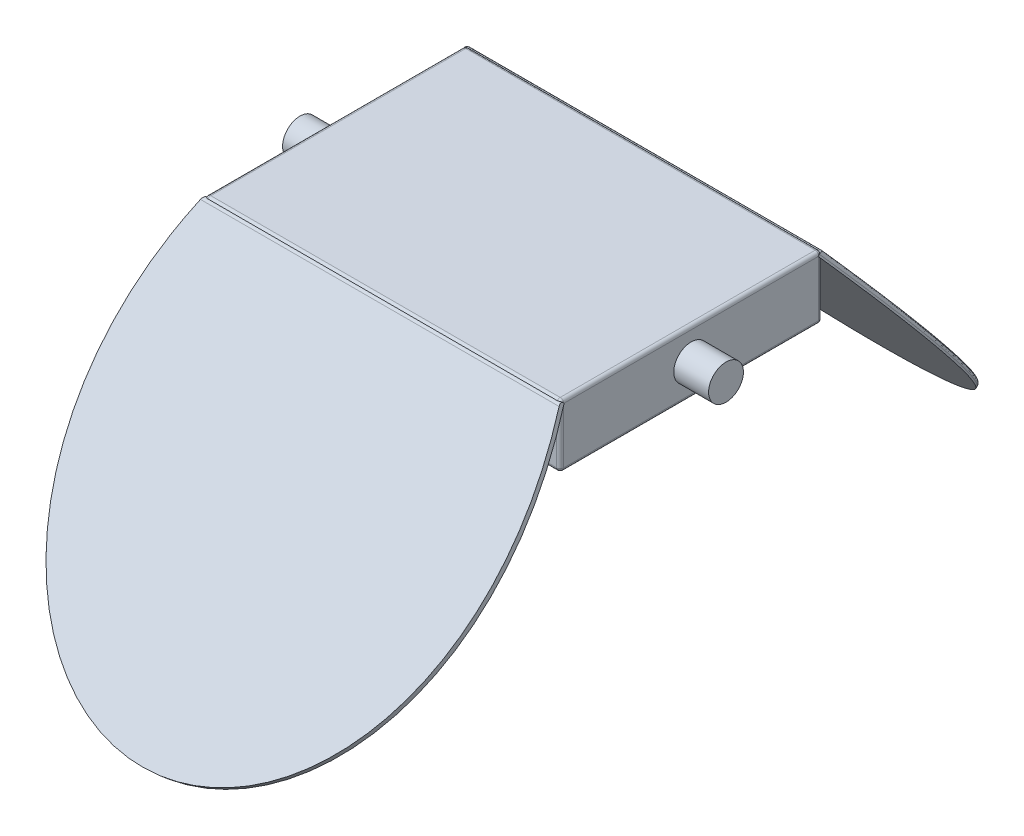
SolidWorks part; units mm, degrees
ref_plane "Front Plane" through (0, 0, 0) normal (0, 0, 1) x (1, 0, 0)
ref_plane "Top Plane" through (0, 0, 0) normal (0, 1, 0) x (1, 0, 0)
ref_plane "Right Plane" through (0, 0, 0) normal (1, 0, 0) x (0, 0, -1)
sketch "Sketch14" plane through (0, 0, 0) normal (0, 1, 0) x (1, 0, 0)
  line L1 (-129.921, -95.504) -> (129.921, -95.504)
  line L2 (-129.921, -95.504) -> (-129.921, 95.504)
  line L3 (-129.921, 95.504) -> (129.921, 95.504)
  line L4 (129.921, -95.504) -> (129.921, 95.504)
  line L5 (-129.921, -95.504) -> (129.921, 95.504) construction
  line L6 (-129.921, 95.504) -> (129.921, -95.504) construction
  point P0 (0, 0)
  dimension "D1" = 191.008
  dimension "D2" = 259.842
extrude "Boss-Extrude1" add sketch "Sketch14" along normal blind 45.72
ref_plane "Plane1" through (0, 65.9169, 78.5568) normal (0, 0.6428, 0.766) x (1, 0, 0)
sketch "Sketch15" plane through (0, 65.9169, 78.5568) normal (0, 0.6428, 0.766) x (1, 0, 0)
  line L1 (-129.921, -26.3652) -> (129.921, -26.3652)
  spline S0 degree 2 poles (129.921, -26.3652) (130.1193, -26.959) (133.7839, -37.9305) (136.4484, -48.414) (139.1256, -58.9474) (140.9759, -69.5188) (142.8478, -80.2142) (143.86, -90.8733) (144.8921, -101.742) (145.0222, -112.4895) (145.1556, -123.5085) (144.3397, -134.3066) (143.5138, -145.2361) (141.723, -155.8378) (139.899, -166.6356) (137.0925, -176.9833) (135.6607, -182.2625) (133.9783, -187.403) (132.2656, -192.6362) (130.2982, -197.7097) (128.3121, -202.8317) (126.0726, -207.7745) (123.8166, -212.754) (121.3108, -217.5351) (118.7774, -222.3688) (115.9974, -226.9827) (113.1758, -231.6657) (110.1105, -236.1049) (106.9856, -240.6304) (103.6196, -244.8844) (100.1934, -249.2145) (96.5317, -253.2451) (92.8443, -257.3039) (88.9341, -261.0412) (84.981, -264.8194) (80.818, -268.2516) (76.5881, -271.7389) (72.1617, -274.852) (67.6438, -278.0296) (62.9439, -280.8011) (58.2169, -283.5885) (53.3307, -285.9502) (48.429, -288.3194) (43.3933, -290.2474) (38.3138, -292.1921) (33.1257, -293.6768) (27.8617, -295.1833) (22.516, -296.2075) (17.109, -297.2434) (11.65, -297.7795) (6.2272, -298.3121) (0.785, -298.348) (-4.6467, -298.3838) (-10.0658, -297.9244) (-15.5064, -297.4632) (-20.9024, -296.5053) (-26.2972, -295.5475) (-31.6157, -294.0986) (-36.8573, -292.6706) (-41.9947, -290.7733) (-47.0851, -288.8934) (-52.045, -286.563) (-56.9862, -284.2413) (-61.7708, -281.4849) (-66.4901, -278.766) (-71.0323, -275.6381) (-75.4942, -272.5655) (-79.7628, -269.1132) (-83.9786, -265.7037) (-87.9856, -261.9399) (-91.9601, -258.2066) (-95.7107, -254.1418) (-99.3966, -250.1471) (-102.85, -245.8495) (-106.2409, -241.6296) (-109.3936, -237.1349) (-112.5034, -232.7014) (-115.3691, -228.0175) (-118.2074, -223.3784) (-120.7956, -218.5109) (-123.3537, -213.7) (-125.6583, -208.6827) (-127.9214, -203.756) (-129.9323, -198.6466) (-131.914, -193.6113) (-133.6445, -188.4143) (-135.3557, -183.2752) (-136.816, -177.9932) (-139.704, -167.5469) (-141.5873, -156.6327) (-143.4236, -145.9904) (-144.2854, -135.0113) (-145.1295, -124.2572) (-145.0305, -113.2783) (-144.9327, -102.4261) (-143.9137, -91.4454) (-142.9118, -80.6477) (-141.0265, -69.809) (-139.1715, -59.1443) (-136.4742, -48.5156) (-133.8009, -37.9814) (-130.1193, -26.959) (-129.921, -26.3652) knots -0.001788 -0.001788 -0.001788 0 0.03125 0.03125 0.0625 0.0625 0.09375 0.09375 0.125 0.125 0.15625 0.15625 0.1875 0.1875 0.21875 0.21875 0.234375 0.234375 0.25 0.25 0.265625 0.265625 0.28125 0.28125 0.296875 0.296875 0.3125 0.3125 0.328125 0.328125 0.34375 0.34375 0.359375 0.359375 0.375 0.375 0.390625 0.390625 0.40625 0.40625 0.421875 0.421875 0.4375 0.4375 0.453125 0.453125 0.46875 0.46875 0.484375 0.484375 0.5 0.5 0.515625 0.515625 0.53125 0.53125 0.546875 0.546875 0.5625 0.5625 0.578125 0.578125 0.59375 0.59375 0.609375 0.609375 0.625 0.625 0.640625 0.640625 0.65625 0.65625 0.671875 0.671875 0.6875 0.6875 0.703125 0.703125 0.71875 0.71875 0.734375 0.734375 0.75 0.75 0.765625 0.765625 0.78125 0.78125 0.8125 0.8125 0.84375 0.84375 0.875 0.875 0.90625 0.90625 0.9375 0.9375 0.96875 0.96875 1 1.001779 1.001779 1.001779
extrude "Boss-Extrude2" add sketch "Sketch15" against normal blind 3.81 separate body
ref_plane "Plane2" through (0, 65.9169, -78.5568) normal (0, 0.6428, -0.766) x (-1, 0, 0)
sketch "Sketch16" plane through (0, 65.9169, -78.5568) normal (0, 0.6428, -0.766) x (-1, 0, 0)
  line L0 (-129.921, -26.3652) -> (129.921, -26.3652)
  spline S0 degree 2 poles (129.921, -26.3652) (130.1193, -26.959) (133.7839, -37.9305) (136.4484, -48.414) (139.1256, -58.9474) (140.9759, -69.5188) (142.8478, -80.2142) (143.86, -90.8733) (144.8921, -101.742) (145.0222, -112.4895) (145.1556, -123.5085) (144.3397, -134.3066) (143.5138, -145.2361) (141.723, -155.8378) (139.899, -166.6356) (137.0925, -176.9833) (135.6607, -182.2625) (133.9783, -187.403) (132.2656, -192.6362) (130.2982, -197.7097) (128.3121, -202.8317) (126.0726, -207.7745) (123.8166, -212.754) (121.3108, -217.5351) (118.7774, -222.3688) (115.9974, -226.9827) (113.1758, -231.6657) (110.1105, -236.1049) (106.9856, -240.6304) (103.6196, -244.8844) (100.1934, -249.2145) (96.5317, -253.2451) (92.8443, -257.3039) (88.9341, -261.0412) (84.981, -264.8194) (80.818, -268.2516) (76.5881, -271.7389) (72.1617, -274.852) (67.6438, -278.0296) (62.9439, -280.8011) (58.2169, -283.5885) (53.3307, -285.9502) (48.429, -288.3194) (43.3933, -290.2474) (38.3138, -292.1921) (33.1257, -293.6768) (27.8617, -295.1833) (22.516, -296.2075) (17.109, -297.2434) (11.65, -297.7795) (6.2272, -298.3121) (0.785, -298.348) (-4.6467, -298.3838) (-10.0658, -297.9244) (-15.5064, -297.4632) (-20.9024, -296.5053) (-26.2972, -295.5475) (-31.6157, -294.0986) (-36.8573, -292.6706) (-41.9947, -290.7733) (-47.0851, -288.8934) (-52.045, -286.563) (-56.9862, -284.2413) (-61.7708, -281.4849) (-66.4901, -278.766) (-71.0323, -275.6381) (-75.4942, -272.5655) (-79.7628, -269.1132) (-83.9786, -265.7037) (-87.9856, -261.9399) (-91.9601, -258.2066) (-95.7107, -254.1418) (-99.3966, -250.1471) (-102.85, -245.8495) (-106.2409, -241.6296) (-109.3936, -237.1349) (-112.5034, -232.7014) (-115.3691, -228.0175) (-118.2074, -223.3784) (-120.7956, -218.5109) (-123.3537, -213.7) (-125.6583, -208.6827) (-127.9214, -203.756) (-129.9323, -198.6466) (-131.914, -193.6113) (-133.6445, -188.4143) (-135.3557, -183.2752) (-136.816, -177.9932) (-139.704, -167.5469) (-141.5873, -156.6327) (-143.4236, -145.9904) (-144.2854, -135.0113) (-145.1295, -124.2572) (-145.0305, -113.2783) (-144.9327, -102.4261) (-143.9137, -91.4454) (-142.9118, -80.6477) (-141.0265, -69.809) (-139.1715, -59.1443) (-136.4742, -48.5156) (-133.8009, -37.9814) (-130.1193, -26.959) (-129.921, -26.3652) knots -0.001788 -0.001788 -0.001788 0 0.03125 0.03125 0.0625 0.0625 0.09375 0.09375 0.125 0.125 0.15625 0.15625 0.1875 0.1875 0.21875 0.21875 0.234375 0.234375 0.25 0.25 0.265625 0.265625 0.28125 0.28125 0.296875 0.296875 0.3125 0.3125 0.328125 0.328125 0.34375 0.34375 0.359375 0.359375 0.375 0.375 0.390625 0.390625 0.40625 0.40625 0.421875 0.421875 0.4375 0.4375 0.453125 0.453125 0.46875 0.46875 0.484375 0.484375 0.5 0.5 0.515625 0.515625 0.53125 0.53125 0.546875 0.546875 0.5625 0.5625 0.578125 0.578125 0.59375 0.59375 0.609375 0.609375 0.625 0.625 0.640625 0.640625 0.65625 0.65625 0.671875 0.671875 0.6875 0.6875 0.703125 0.703125 0.71875 0.71875 0.734375 0.734375 0.75 0.75 0.765625 0.765625 0.78125 0.78125 0.8125 0.8125 0.84375 0.84375 0.875 0.875 0.90625 0.90625 0.9375 0.9375 0.96875 0.96875 1 1.001779 1.001779 1.001779
extrude "Boss-Extrude3" add sketch "Sketch16" against normal blind 3.81 separate body
sketch "Sketch20" plane through (-129.921, 0, 0) normal (-1, 0, 0) x (0, 0, 1)
  line L0 (-95.504, 22.86) -> (95.504, 22.86) construction
  line L1 (-95.504, 45.72) -> (-95.504, 0) construction
  line L2 (95.504, 45.72) -> (95.504, 0) construction
  line L3 (0, 0) -> (0, 45.72) construction
  line L4 (-95.504, 45.72) -> (95.504, 45.72) construction
  circle A0 centre (0, 22.86) radius 12.7
extrude "Boss-Extrude4" add sketch "Sketch20" along normal blind 25.4
sketch "Sketch21" plane through (129.921, 0, 0) normal (1, 0, 0) x (0, 0, -1)
  line L0 (-95.504, 22.86) -> (95.504, 22.86) construction
  line L1 (-95.504, 45.72) -> (-95.504, 0) construction
  line L2 (95.504, 45.72) -> (95.504, 0) construction
  line L3 (0, 45.72) -> (0, 0) construction
  line L4 (-95.504, 45.72) -> (95.504, 45.72) construction
  circle A0 centre (0, 22.86) radius 12.7
extrude "Boss-Extrude5" add sketch "Sketch21" along normal blind 25.4
fillet "Fillet1" radius 2.54 2 edges
fillet "Fillet2" radius 2.54 1 edges at (0, 45.72, -95.504)
fillet "Fillet3" radius 2.54 1 edges at (0, 45.72, 95.504)
fillet "Fillet4" radius 2.54 1 edges
fillet "Fillet5" radius 2.54 10 edges at (-129.921, 21.59, -95.504) (-129.921, 44.9761, -94.7601) (-129.921, 21.59, 95.504) (-129.921, 44.9761, 94.7601) (129.921, 21.59, 95.504) (129.921, 44.9761, 94.7601) (129.921, 21.59, -95.504) (129.921, 44.9761, -94.7601) (-129.921, 45.72, 0) (129.921, 45.72, 0)
fillet "Fillet6" radius 2.54 8 edges at (129.1771, 0, 94.7601) (0, 0, 95.504) (-129.1771, 0, 94.7601) (-129.1771, 0, -94.7601) (0, 0, -95.504) (129.1771, 0, -94.7601) (-129.921, 0, 0) (129.921, 0, 0)
